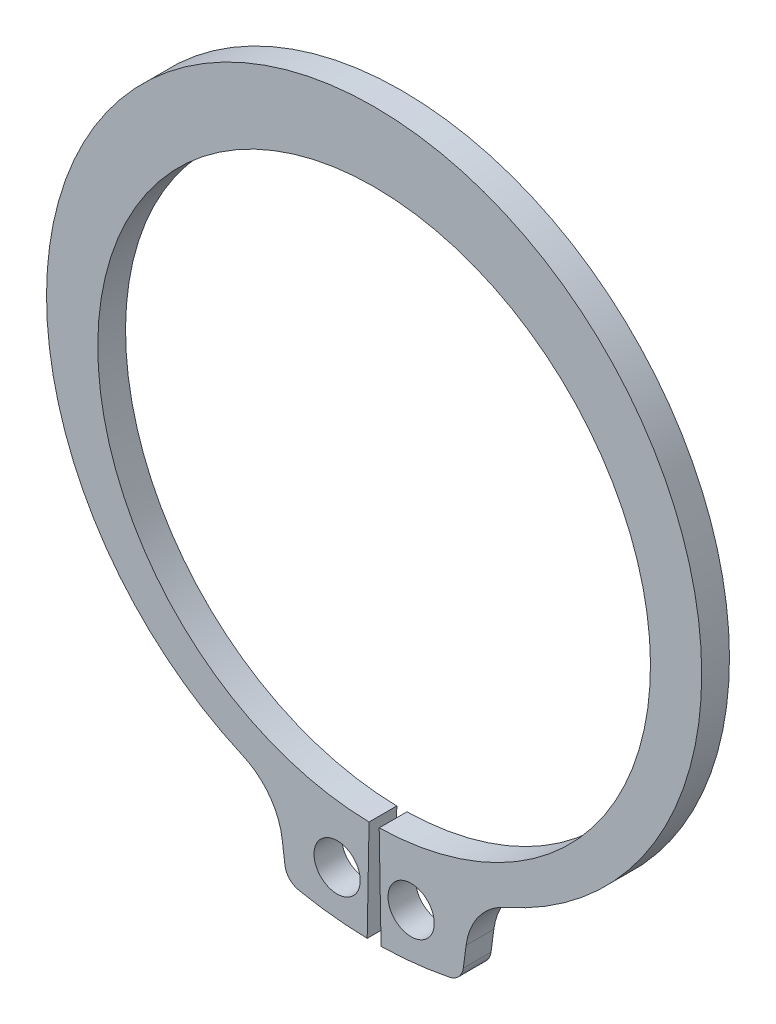
SolidWorks part; units mm, degrees
ref_plane "Plane1" through (0, 0, 0) normal (0, 0, 1) x (1, 0, 0)
ref_plane "Plane2" through (0, 0, 0) normal (0, 1, 0) x (1, 0, 0)
ref_plane "Plane3" through (0, 0, 0) normal (1, 0, 0) x (0, 0, -1)
sketch "Clipboard" plane through (0, 0, 0) normal (0, 0, 1) x (1, 0, 0)
  line L0 (0, 0) -> (3, 0)
  line L1 (0, 0) -> (0, 1.5)
  line L2 (0, 0) -> (0, -4.4)
  circle A0 centre (0, 0) radius 1
  circle A1 centre (0, 0) radius 12.5
  dimension "HoleDia" = 2
  dimension "ShaftDia" = 25
  dimension "LargeSection" = 3
  dimension "SmallSection" = 1.5
  dimension "LugSection" = 4.4
sketch "BodySke" plane through (0, 0, 0) normal (0, 0, 1) x (1, 0, 0)
  line L0 (-1.5431, 0) -> (1.5431, 0) construction
  line L1 (0, 0) -> (0, 14.95) construction
  line L2 (0.2193, -11.948) -> (0.3, -16.3472)
  line L3 (-0.2193, -11.948) -> (-0.3, -16.3472)
  line L4 (0, 0) -> (6.8515, -14.8452) construction
  line L5 (0, 0) -> (-6.8515, -14.8452) construction
  line L7 (3.9769, -14.4667) -> (3.8561, -15.3842)
  line L8 (-3.9769, -14.4667) -> (-3.8561, -15.3842)
  circle A0 centre (0, 0) radius 11.95 construction
  arc A1 (0.2193, -11.948) -> (-0.2193, -11.948) centre (0, 0) ccw
  arc A2 (5.6362, -12.2121) -> (-5.6362, -12.2121) centre (0, 0.7842) ccw construction
  arc A3 (0.3, -16.3472) -> (3.2622, -16.0213) centre (0, 0) ccw
  arc A4 (5.6874, -12.1898) -> (3.9769, -14.4667) centre (6.8515, -14.8452) ccw
  arc A5 (-3.9769, -14.4667) -> (-5.6874, -12.1898) centre (-6.8515, -14.8452) ccw
  arc A6 (-3.2622, -16.0213) -> (-0.3, -16.3472) centre (0, 0) ccw
  arc A7 (5.6874, -12.1898) -> (-5.6874, -12.1898) centre (0, 0.7842) ccw
  arc A8 (-4.0592, -13.8421) -> (4.0592, -13.8421) centre (0, 0) ccw construction
  circle A9 centre (1.6, -14.336) radius 1
  circle A10 centre (-1.6, -14.336) radius 1
  arc A11 (3.8561, -15.3842) -> (3.2622, -16.0213) centre (3.1126, -15.2863) cw
  arc A12 (-3.8561, -15.3842) -> (-3.2622, -16.0213) centre (-3.1126, -15.2863) ccw
  point P28 (3.7876, -15.9052)
  point P31 (-3.7876, -15.9052)
  dimension "HoleDia" = 2
  dimension "GrooveDia" = 23.9
  dimension "LugRad" = 16.35
  dimension "HoleOffsetRad" = 14.425
  dimension "D3" = 0.75
  dimension "LargeRad" = 14.95
  dimension "SmallRad" = 13.45
  dimension "SmallAngle" = 49.549
  dimension "D2" = 15
  dimension "HoleSpacing" = 3.2
  dimension "Gap" = 0.6
extrude "Body" add sketch "BodySke" against normal blind 1.2
sketch "NotSke" plane through (0, 0, 0) normal (0, 0, 1) x (1, 0, 0)
  line L0 (1.6, -13.336) -> (1.6, -15.336)
  line L1 (1.6, -15.336) -> (-1.6, -15.336)
  line L2 (-1.6, -15.336) -> (-1.6, -13.336)
  line L3 (-1.6, -13.336) -> (1.6, -13.336)
  circle A0 centre (1.6, -14.336) radius 1 construction
  circle A1 centre (-1.6, -14.336) radius 1 construction
extrude "Notch" [suppressed] cut sketch "NotSke" against normal through all
sketch "UnlSke" plane through (0, 0, 0) normal (0, 0, 1) x (1, 0, 0)
  line L0 (-2.9356, -16.0843) -> (-2.1456, -11.7558)
  line L1 (2.9356, -16.0843) -> (2.1456, -11.7558)
  arc A0 (2.1456, -11.7558) -> (-2.1456, -11.7558) centre (0, 0) ccw
  arc A1 (2.9356, -16.0843) -> (-2.9356, -16.0843) centre (0, 0) ccw
  arc A2 (0.3, -16.3472) -> (3.2622, -16.0213) centre (0, 0) ccw construction
  arc A3 (0.2193, -11.948) -> (-0.2193, -11.948) centre (0, 0) ccw construction
  circle A4 centre (-1.6, -14.336) radius 1 construction
  circle A5 centre (1.6, -14.336) radius 1 construction
extrude "Unlug" [suppressed] add sketch "UnlSke" against normal through all
equation "' \"ShaftDia@Clipboard\" = 3"
equation "' \"Thickness@Body\" = 0.4"
equation "' \"GrooveDia@BodySke\" = 2.8"
equation "' \"LugSection@Clipboard\" = 1.9"
equation "' \"LargeSection@Clipboard\" = 0.8"
equation "' \"HoleDia@Clipboard\" = 1.0"
equation "' \"ShaftDia@Clipboard\" = 10"
equation "' \"Thickness@Body\" = 1.0"
equation "' \"GrooveDia@BodySke\" = 9.6"
equation "' \"LugSection@Clipboard\" = 3.3"
equation "' \"LargeSection@Clipboard\" = 1.8"
equation "' \"HoleDia@Clipboard\" = 1.5"
equation "\"SmallSection@Clipboard\" = \"LargeSection@Clipboard\" * 0.5"
equation "\"Gap@BodySke\" =  \"Thickness@Body\" / 2"
equation "\"LargeRad@BodySke\" =  \"GrooveDia@BodySke\" / 2 +  \"LargeSection@Clipboard\""
equation "\"SmallRad@BodySke\" =  \"GrooveDia@BodySke\" / 2 +  \"SmallSection@Clipboard\""
equation "\"LugRad@BodySke\" = \"GrooveDia@BodySke\" / 2 + \"LugSection@Clipboard\""
equation "\"HoleOffsetRad@BodySke\" = (  \"ShaftDia@Clipboard\" / 2 + \"LugRad@BodySke\" ) / 2"
equation "\"HoleSpacing@BodySke\" = \"Gap@BodySke\"  * 2 +  \"HoleDia@Clipboard\""
equation "\"HoleDia@BodySke\" =  \"HoleDia@Clipboard\""
equation "\"SmallAngle@BodySke\" = atn(\"HoleSpacing@BodySke\" / 2 / sqr(\"HoleOffsetRad@BodySke\"  * \"HoleOffsetRad@BodySke\" - (\"HoleSpacing@BodySke\" / 2) * (\"HoleSpacing@BodySke\" / 2) ))  * 7 *  (\"LargeRad@BodySke\" / \"SmallRad@BodySke\")* ( 180 / 3.141593)"
